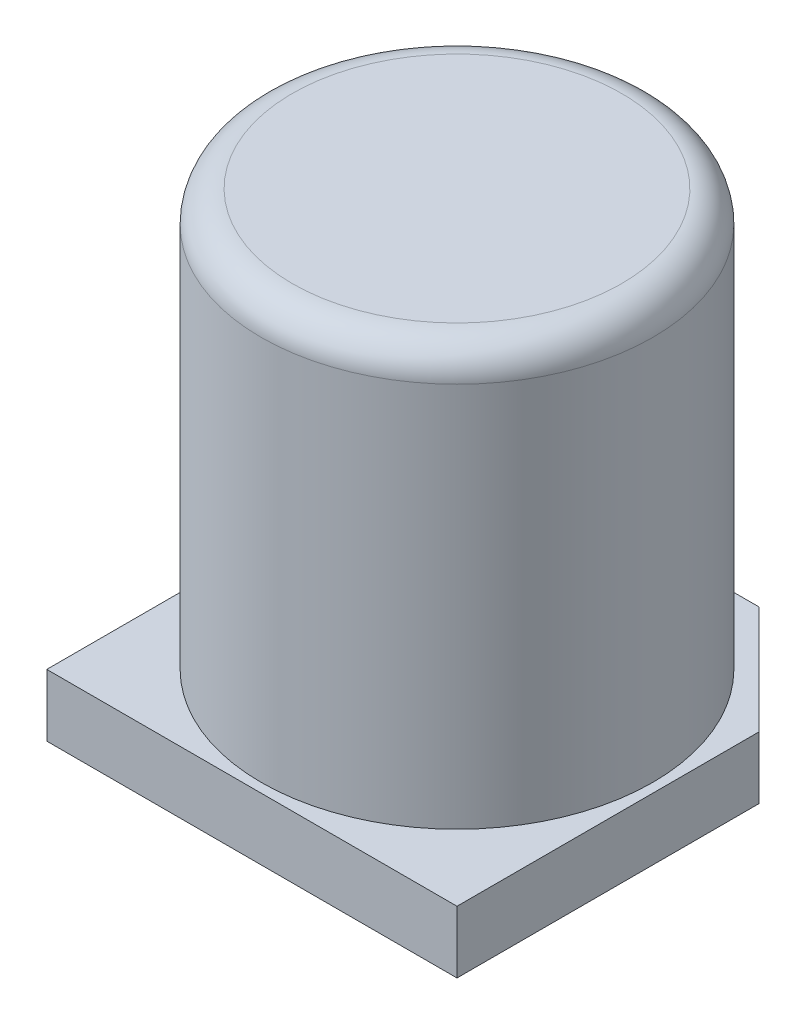
SolidWorks part; units mm, degrees
ref_plane "Plano frontal" through (0, 0, 0) normal (0, 0, 1) x (1, 0, 0)
ref_plane "Plano superior" through (0, 0, 0) normal (0, 1, 0) x (1, 0, 0)
ref_plane "Plano direito" through (0, 0, 0) normal (1, 0, 0) x (0, 0, -1)
ref_plane "Plano1" through (0, 0, 0) normal (0, -1, 0) x (1, 0, 0)
sketch "Esboço1" plane through (0, 0, 0) normal (0, -1, 0) x (1, 0, 0)
  line L0 (-3.3, 3.3) -> (-3.3, -3.3)
  line L1 (-3.3, -3.3) -> (3.3, -3.3)
  line L2 (3.3, -3.3) -> (3.3, 3.3)
  line L3 (3.3, 3.3) -> (-3.3, 3.3)
extrude "Ressalto-extrusão1" add sketch "Esboço1" against normal blind 1
sketch "Esboço2" plane through (0, 0, 0) normal (0, 0, 1) x (1, 0, 0)
  line L0 (3.15, 7.7) -> (0, 7.7)
  line L1 (0, 7.7) -> (0, 1)
  line L2 (0, 1) -> (3.15, 1)
  line L3 (3.15, 1) -> (3.15, 7.7)
  line L4 (0, 7.7) -> (0, 1) construction
revolve "Revolução1" add sketch "Esboço2" angle 360 about L4
chamfer "Chanfro1" distance 1.7375 angle 45 2 edges at (3.3, 0.5, -3.3) (-3.3, 0.5, -3.3)
fillet "Filete1" radius 0.5 1 edges at (0, 7.7, -3.15)
